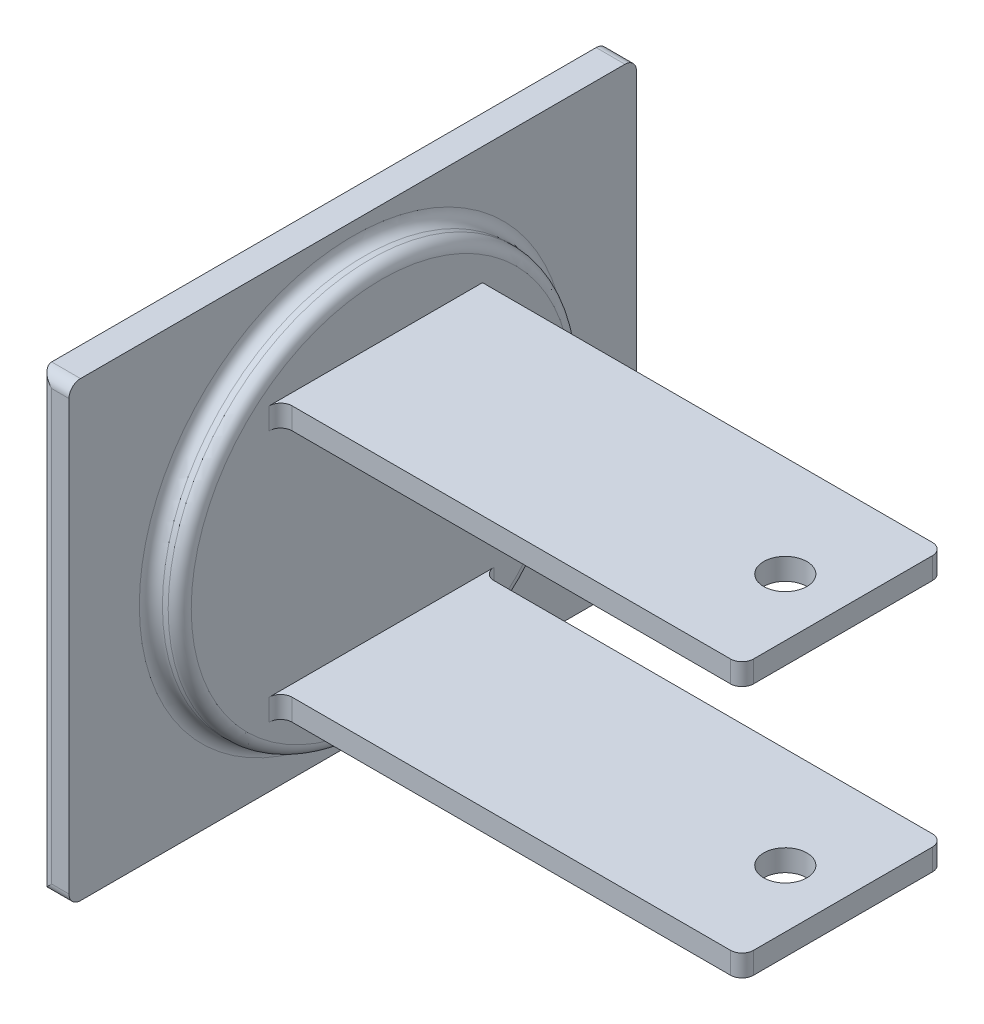
SolidWorks part; units mm, degrees
ref_plane "Front Plane" through (0, 0, 0) normal (0, 0, 1) x (1, 0, 0)
ref_plane "Top Plane" through (0, 0, 0) normal (0, 1, 0) x (1, 0, 0)
ref_plane "Right Plane" through (0, 0, 0) normal (1, 0, 0) x (0, 0, -1)
sketch "Sketch1" plane through (0, 0, 0) normal (1, 0, 0) x (0, 0, -1)
  line L1 (0, 0) -> (124.968, 0)
  line L2 (0, 0) -> (0, 99.568)
  line L3 (0, 99.568) -> (124.968, 99.568)
  line L4 (124.968, 0) -> (124.968, 99.568)
  dimension "D1" = 124.968
  dimension "D2" = 99.568
extrude "Boss-Extrude1" add sketch "Sketch1" along normal blind 6.35
sketch "Sketch2" plane through (6.35, 0, 0) normal (1, 0, 0) x (0, 0, -1)
  line L0 (0, 99.568) -> (124.968, 0) construction
  circle A0 centre (62.484, 49.784) radius 44.45
  dimension "D1" = 88.9
extrude "Boss-Extrude2" add sketch "Sketch2" along normal blind 6.35
sketch "Sketch3" plane through (12.7, 0, 0) normal (1, 0, 0) x (0, 0, -1)
  line L0 (62.484, 49.784) -> (62.484, 94.234) construction
  line L1 (62.484, 49.784) -> (88.5379, 49.784) construction
  line L2 (40.259, 79.9465) -> (84.709, 79.9465)
  line L3 (40.259, 79.9465) -> (40.259, 75.184)
  line L4 (40.259, 75.184) -> (84.709, 75.184)
  line L5 (84.709, 79.9465) -> (84.709, 75.184)
  line L6 (40.259, 79.9465) -> (84.709, 75.184) construction
  line L7 (40.259, 75.184) -> (84.709, 79.9465) construction
  line L9 (40.259, 19.6215) -> (84.709, 19.6215)
  line L10 (40.259, 19.6215) -> (40.259, 24.384)
  line L11 (40.259, 24.384) -> (84.709, 24.384)
  line L12 (84.709, 19.6215) -> (84.709, 24.384)
  line L13 (40.259, 19.6215) -> (84.709, 24.384) construction
  line L14 (40.259, 24.384) -> (84.709, 19.6215) construction
  circle A0 centre (62.484, 49.784) radius 44.45 construction
  point P0 (62.484, 77.5653)
  point P10 (62.484, 22.0027)
  dimension "D1" = 25.4
  dimension "D2" = 4.7625
  dimension "D3" = 44.45
  dimension "D4" = 25.4
extrude "Boss-Extrude3" add sketch "Sketch3" along normal blind 101.6
sketch "Sketch4" plane through (0, 19.6215, 0) normal (0, -1, 0) x (1, 0, 0)
  line L0 (114.3, -40.259) -> (114.3, -84.709) construction
  circle A0 centre (101.6, -62.484) radius 4.7625
  dimension "D1" = 9.525
  dimension "D2" = 12.7
extrude "Cut-Extrude1" cut sketch "Sketch4" against normal through all
fillet "Fillet1" radius 2.54 14 edges at (6.35, 49.784, -18.034) (0, 49.784, 0) (12.7, 49.784, -106.934) (12.7, 22.0027, -84.709) (12.7, 22.0027, -40.259) (12.7, 77.5653, -40.259) (114.3, 77.5653, -40.259) (114.3, 22.0027, -40.259) (114.3, 22.0027, -84.709) (3.175, 0, 0) (114.3, 77.5653, -84.709) (3.175, 0, -124.968) (3.175, 99.568, 0) (3.175, 99.568, -124.968)
